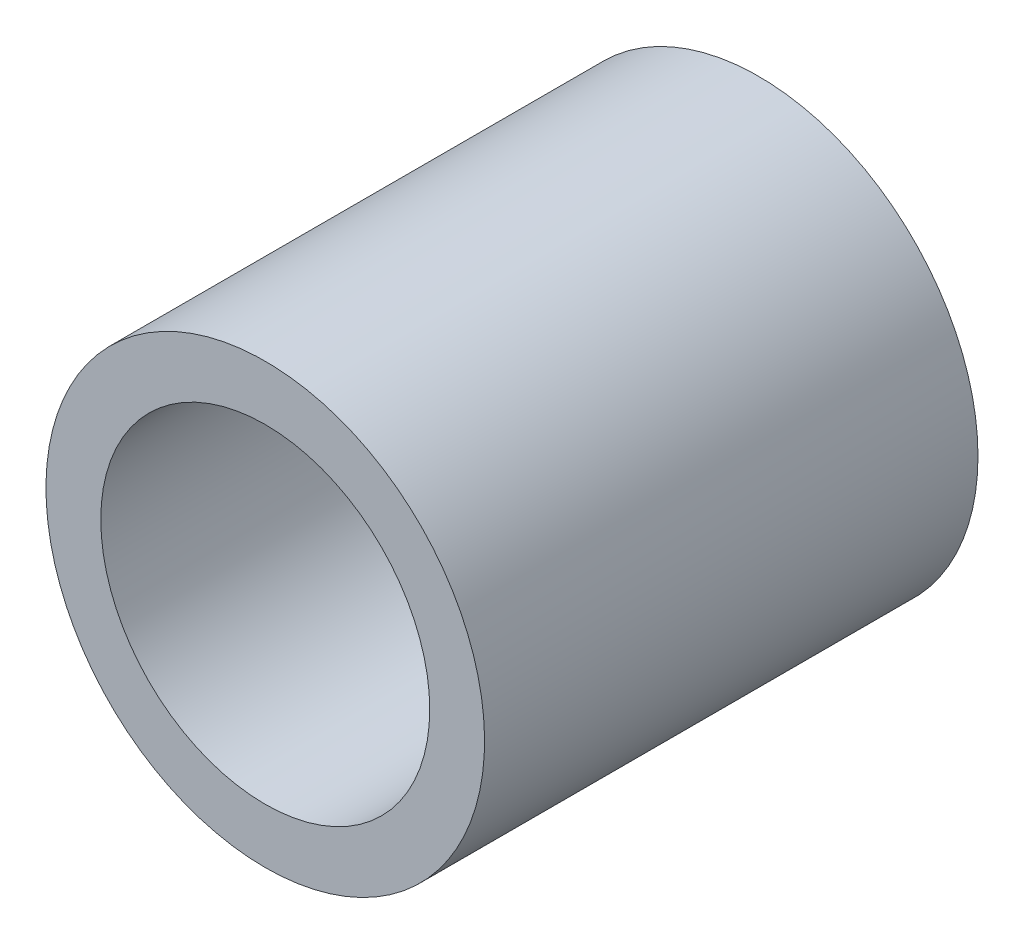
SolidWorks part; units mm, degrees
ref_plane "Plane1" through (0, 0, 0) normal (0, 0, 1) x (1, 0, 0)
ref_plane "Plane2" through (0, 0, 0) normal (0, 1, 0) x (1, 0, 0)
ref_plane "Plane3" through (0, 0, 0) normal (1, 0, 0) x (0, 0, -1)
other "Configuration Table"
sketch "Sketch1" plane through (0, 0, 0) normal (0, 0, 1) x (1, 0, 0)
  circle A0 centre (0, 0) radius 12.7
  dimension "D1" = 25.4
extrude "Base-Extrude" add sketch "Sketch1" along normal up to surface (28.575 mm away)
sketch "Sketch2" plane through (0, 0, 28.575) normal (0, 0, 1) x (1, 0, 0)
  circle A0 centre (0, 0) radius 9.525
  dimension "D1" = 19.05
extrude "Cut-Extrude1" cut sketch "Sketch2" against normal through all
